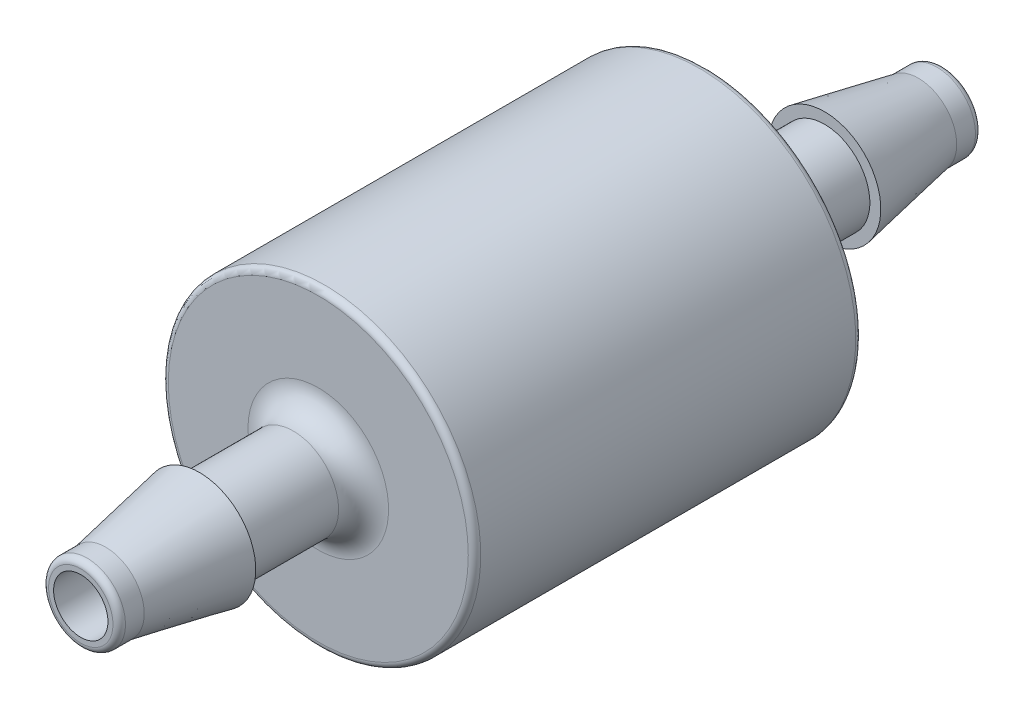
SolidWorks part; units mm, degrees
material "Petg 30% Infill"
ref_plane "Front Plane" through (0, 0, 0) normal (0, 0, 1) x (1, 0, 0)
ref_plane "Top Plane" through (0, 0, 0) normal (0, 1, 0) x (1, 0, 0)
ref_plane "Right Plane" through (0, 0, 0) normal (1, 0, 0) x (0, 0, -1)
sketch "Sketch1" plane through (0, 0, 0) normal (1, 0, 0) x (0, 0, -1)
  line L0 (-17.526, 0) -> (17.526, 0) construction
  line L1 (17.526, 6.35) -> (17.526, -6.35) construction
  line L2 (-17.526, 1.1049) -> (-17.526, -1.1049) construction
  line L4 (-17.526, 1.5875) -> (-17.526, -1.5875) construction
  line L8 (-17.526, 6.35) -> (-17.526, -6.35) construction
  point P20 (-7.874, 0)
  point P21 (7.874, 0)
  dimension "OD" = 12.7
  dimension "Lg." = 35.052
  dimension "ID" = 2.2098
  dimension "L1" = 9.652
  dimension "L2" = 15.748
  dimension "L3" = 9.652
  dimension "Tube ID" = 3.175
sketch "Sketch2" plane through (0, 0, 0) normal (1, 0, 0) x (0, 0, -1)
  line L0 (17.526, 0) -> (-17.526, 0) construction
  line L1 (17.526, 6.35) -> (17.526, -6.35) construction
  line L2 (-17.526, 1.1049) -> (-17.526, -1.1049) construction
  line L3 (-17.526, 1.1049) -> (-17.526, 1.3081)
  line L4 (12.7, 1.8415) -> (8.89, 1.8415)
  line L5 (17.272, 1.5621) -> (16.51, 1.5621)
  line L6 (7.874, 2.8575) -> (7.874, 6.096)
  line L7 (17.526, 1.1049) -> (17.526, 1.3081)
  line L8 (-7.874, 2.8575) -> (-7.874, 6.096)
  line L9 (-7.62, 6.35) -> (7.62, 6.35)
  line L10 (12.7, 2.286) -> (12.7, 1.8415)
  line L11 (16.51, 1.5621) -> (12.7, 2.286)
  line L14 (0, 0) -> (0, 6.35) construction
  line L15 (-17.272, 1.5621) -> (-16.51, 1.5621)
  line L17 (-16.51, 1.5621) -> (-12.7, 2.286)
  line L18 (-12.7, 2.286) -> (-12.7, 1.8415)
  line L19 (-12.7, 1.8415) -> (-8.89, 1.8415)
  line L24 (-17.526, 1.1049) -> (17.526, 1.1049)
  arc A0 (7.874, 6.096) -> (7.62, 6.35) centre (7.62, 6.096) ccw
  arc A1 (-7.874, 6.096) -> (-7.62, 6.35) centre (-7.62, 6.096) cw
  arc A2 (-17.272, 1.5621) -> (-17.526, 1.3081) centre (-17.272, 1.3081) ccw
  arc A3 (17.272, 1.5621) -> (17.526, 1.3081) centre (17.272, 1.3081) cw
  arc A4 (-8.89, 1.8415) -> (-7.874, 2.8575) centre (-8.89, 2.8575) ccw
  arc A5 (8.89, 1.8415) -> (7.874, 2.8575) centre (8.89, 2.8575) cw
  dimension "D3" = 4.572
  dimension "D4" = 3.81
  dimension "D5" = 3.683
  dimension "R1" = 0.254
  dimension "R2" = 0.254
  dimension "R3" = 1.016
  dimension "D1" = 3.1242
  dimension "D2" = 1.016
revolve "Revolve1" add sketch "Sketch2" angle 360 mid plane about L0
sketch "SketchX" plane through (0, 0, 0) normal (1, 0, 0) x (0, 0, -1)
  line L10 (17.526, 1.1049) -> (-17.526, 1.1049) construction
  line L12 (-17.526, -1.1049) -> (17.526, -1.1049) construction
  line L13 (17.526, 1.1049) -> (-17.526, 1.1049)
  line L14 (-17.526, -1.1049) -> (17.526, -1.1049)
